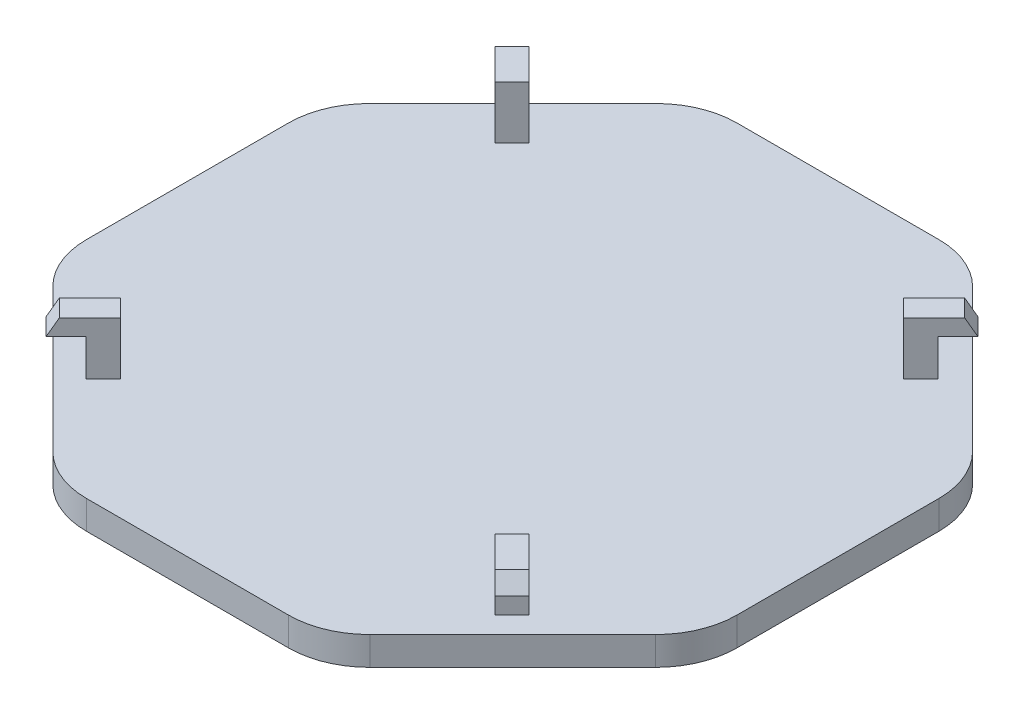
SolidWorks part; units mm, degrees
ref_plane "Front Plane" through (0, 0, 0) normal (0, 0, 1) x (1, 0, 0)
ref_plane "Top Plane" through (0, 0, 0) normal (0, 1, 0) x (1, 0, 0)
ref_plane "Right Plane" through (0, 0, 0) normal (1, 0, 0) x (0, 0, -1)
sketch "Sketch1" plane through (0, 0, 0) normal (0, 1, 0) x (1, 0, 0)
  line L1 (40, 16.5685) -> (16.5685, 40)
  line L2 (16.5685, 40) -> (-16.5685, 40)
  line L3 (-16.5685, 40) -> (-40, 16.5685)
  line L4 (-40, 16.5685) -> (-40, -16.5685)
  line L5 (-40, -16.5685) -> (-16.5685, -40)
  line L6 (-16.5685, -40) -> (16.5685, -40)
  line L7 (16.5685, -40) -> (40, -16.5685)
  line L8 (40, -16.5685) -> (40, 16.5685)
  circle A0 centre (0, 0) radius 40 construction
  point P1 (0, 40)
  dimension "D1" = 80
extrude "Boss-Extrude1" add sketch "Sketch1" along normal blind 3.5
fillet "Fillet1" radius 10 8 edges at (-40, 1.75, -16.5685) (-16.5685, 1.75, -40) (16.5685, 1.75, -40) (40, 1.75, -16.5685) (-40, 1.75, 16.5685) (40, 1.75, 16.5685) (16.5685, 1.75, 40) (-16.5685, 1.75, 40)
ref_plane "Plane1" through (0, 0, 0) normal (-0.7071, 0, -0.7071) x (-0.7071, 0, 0.7071)
sketch "Sketch3" plane through (0, 0, 0) normal (-0.7071, 0, -0.7071) x (-0.7071, 0, 0.7071)
  line L0 (-33.97, 3.5) -> (-33.97, 10)
  line L1 (-37.0711, 3.5) -> (-19.4975, 3.5) construction
  line L2 (-33.97, 10) -> (-39.3153, 10)
  line L3 (-39.3153, 10) -> (-40.47, 8)
  line L4 (-40.47, 8) -> (-36.97, 8)
  line L5 (-36.97, 8) -> (-36.97, 3.5)
  line L6 (-36.97, 3.5) -> (-33.97, 3.5)
  line L7 (-40, 0) -> (-40, 3.5) construction
  dimension "D1" = 3.03
  dimension "D2" = 3
  dimension "D3" = 3.5
  dimension "D4" = 60
  dimension "D5" = 4.5
  dimension "D6" = 6.5
extrude "Boss-Extrude2" add sketch "Sketch3" along normal blind 1.5 and the other way blind 1.5
pattern_circular "CirPattern1" count 4 over 360 about axis through (-0.0428, 0, 0.0428) along (0, 1, 0) of "Boss-Extrude2"
